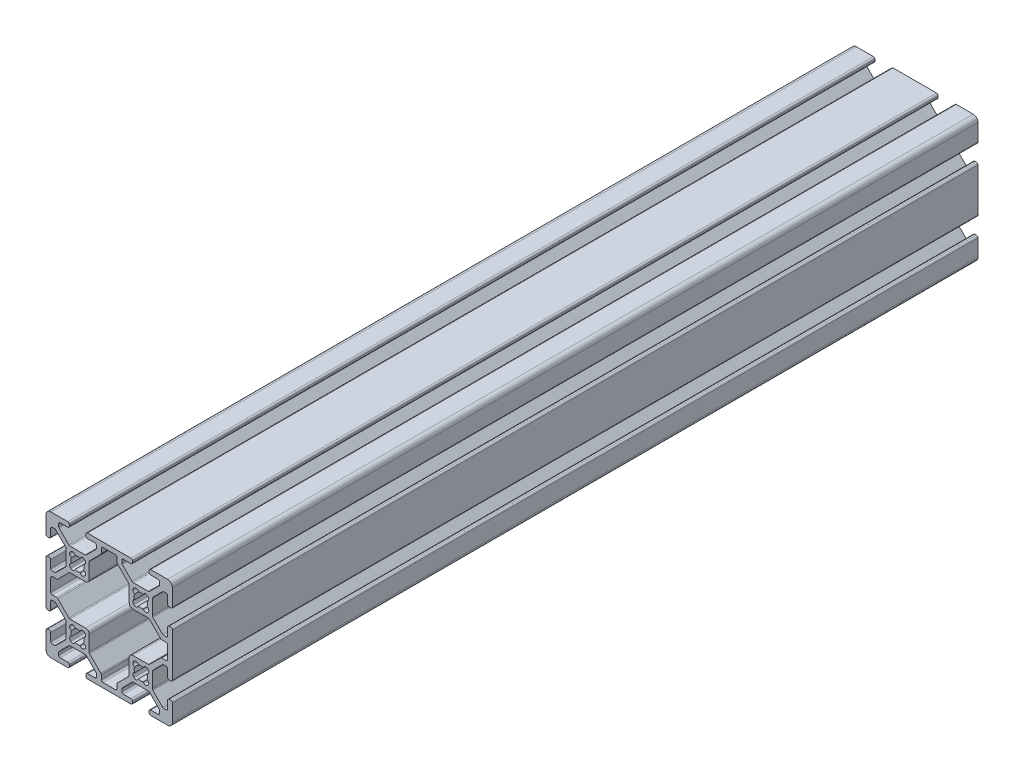
SolidWorks part; units mm, degrees
material "6105-T5 Aluminum"
ref_plane "Front Plane" through (0, 0, 0) normal (0, 0, 1) x (1, 0, 0)
ref_plane "Top Plane" through (0, 0, 0) normal (0, 1, 0) x (1, 0, 0)
ref_plane "Right Plane" through (0, 0, 0) normal (1, 0, 0) x (0, 0, -1)
sketch "Sketch1" plane through (0, 0, 0) normal (0, 0, 1) x (1, 0, 0)
  line L0 (-2.1249, 17.6955) -> (-2.3045, 17.8751)
  line L1 (-2.3045, 22.1249) -> (-2.1249, 22.3045)
  line L2 (2.1249, 22.3045) -> (2.3045, 22.1249)
  line L3 (2.3045, 17.8751) -> (2.1249, 17.6955)
  line L4 (-22.1249, 17.6955) -> (-22.3045, 17.8751)
  line L5 (-22.3045, 22.1249) -> (-22.1249, 22.3045)
  line L6 (-17.8751, 22.3045) -> (-17.6955, 22.1249)
  line L7 (-17.6955, 17.8751) -> (-17.8751, 17.6955)
  line L8 (-2.1249, -2.3045) -> (-2.3045, -2.1249)
  line L9 (-2.3045, 2.1249) -> (-2.1249, 2.3045)
  line L10 (2.1249, 2.3045) -> (2.3045, 2.1249)
  line L11 (2.3045, -2.1249) -> (2.1249, -2.3045)
  line L12 (-12.505, -7.992) -> (-12.505, -6.6448)
  line L13 (-12.6538, -6.2856) -> (-16.1962, -2.7431)
  line L14 (-16.345, -2.3839) -> (-16.345, 2.512)
  line L15 (-17.488, 3.655) -> (-22.3839, 3.655)
  line L16 (-22.7431, 3.8038) -> (-26.2856, 7.3462)
  line L17 (-26.6448, 7.495) -> (-27.992, 7.495)
  line L18 (-28.5, 8.003) -> (-28.5, 11.997)
  line L19 (-27.992, 12.505) -> (-26.6448, 12.505)
  line L20 (-26.2856, 12.6538) -> (-22.7431, 16.1962)
  line L21 (-22.3839, 16.345) -> (-17.488, 16.345)
  line L22 (-16.345, 17.488) -> (-16.345, 22.3839)
  line L23 (-16.1962, 22.7431) -> (-12.6538, 26.2856)
  line L24 (-12.505, 26.6448) -> (-12.505, 27.992)
  line L25 (-11.997, 28.5) -> (-8.003, 28.5)
  line L26 (-7.495, 27.992) -> (-7.495, 26.6448)
  line L27 (-7.3462, 26.2856) -> (-3.8038, 22.7431)
  line L28 (-3.655, 22.3839) -> (-3.655, 17.488)
  line L29 (-2.512, 16.345) -> (2.3839, 16.345)
  line L30 (2.7431, 16.1962) -> (6.2856, 12.6538)
  line L31 (6.6448, 12.505) -> (7.992, 12.505)
  line L32 (8.5, 11.997) -> (8.5, 8.003)
  line L33 (7.992, 7.495) -> (6.6448, 7.495)
  line L34 (6.2856, 7.3462) -> (2.7431, 3.8038)
  line L35 (2.3839, 3.655) -> (-2.512, 3.655)
  line L36 (-3.655, 2.512) -> (-3.655, -2.3839)
  line L37 (-3.8038, -2.7431) -> (-7.3462, -6.2856)
  line L38 (-7.495, -6.6448) -> (-7.495, -7.992)
  line L39 (-8.003, -8.5) -> (-11.997, -8.5)
  line L40 (-22.1249, -2.3045) -> (-22.3045, -2.1249)
  line L41 (-22.3045, 2.1249) -> (-22.1249, 2.3045)
  line L42 (-17.8751, 2.3045) -> (-17.6955, 2.1249)
  line L43 (-17.6955, -2.1249) -> (-17.8751, -2.3045)
  line L44 (-22.3839, -3.655) -> (-17.6161, -3.655)
  line L45 (-17.2569, -3.8038) -> (-14.1538, -6.9069)
  line L46 (-14.005, -7.2661) -> (-14.005, -7.992)
  line L47 (-14.513, -8.5) -> (-16.862, -8.5)
  line L48 (-17.37, -9.008) -> (-17.37, -9.492)
  line L49 (-16.862, -10) -> (-3.138, -10)
  line L50 (-2.63, -9.492) -> (-2.63, -9.008)
  line L51 (-3.138, -8.5) -> (-5.487, -8.5)
  line L52 (-5.995, -7.992) -> (-5.995, -7.2661)
  line L53 (-5.8462, -6.9069) -> (-2.7431, -3.8038)
  line L54 (-2.3839, -3.655) -> (2.3839, -3.655)
  line L55 (2.7431, -3.8038) -> (5.8462, -6.9069)
  line L56 (5.995, -7.2661) -> (5.995, -7.992)
  line L57 (5.487, -8.5) -> (3.138, -8.5)
  line L58 (2.63, -9.008) -> (2.63, -9.492)
  line L59 (3.138, -10) -> (8.5, -10)
  line L60 (10, -8.5) -> (10, -3.138)
  line L61 (9.492, -2.63) -> (9.008, -2.63)
  line L62 (8.5, -3.138) -> (8.5, -5.487)
  line L63 (7.992, -5.995) -> (7.2661, -5.995)
  line L64 (6.9069, -5.8462) -> (3.8038, -2.7431)
  line L65 (3.655, -2.3839) -> (3.655, 2.3839)
  line L66 (3.8038, 2.7431) -> (6.9069, 5.8462)
  line L67 (7.2661, 5.995) -> (7.992, 5.995)
  line L68 (8.5, 5.487) -> (8.5, 3.138)
  line L69 (9.008, 2.63) -> (9.492, 2.63)
  line L70 (10, 3.138) -> (10, 16.862)
  line L71 (9.492, 17.37) -> (9.008, 17.37)
  line L72 (8.5, 16.862) -> (8.5, 14.513)
  line L73 (7.992, 14.005) -> (7.2661, 14.005)
  line L74 (6.9069, 14.1538) -> (3.8038, 17.2569)
  line L75 (3.655, 17.6161) -> (3.655, 22.3839)
  line L76 (3.8038, 22.7431) -> (6.9069, 25.8462)
  line L77 (7.2661, 25.995) -> (7.992, 25.995)
  line L78 (8.5, 25.487) -> (8.5, 23.138)
  line L79 (9.008, 22.63) -> (9.492, 22.63)
  line L80 (10, 23.138) -> (10, 28.5)
  line L81 (8.5, 30) -> (3.138, 30)
  line L82 (2.63, 29.492) -> (2.63, 29.008)
  line L83 (3.138, 28.5) -> (5.487, 28.5)
  line L84 (5.995, 27.992) -> (5.995, 27.2661)
  line L85 (5.8462, 26.9069) -> (2.7431, 23.8038)
  line L86 (2.3839, 23.655) -> (-2.3839, 23.655)
  line L87 (-2.7431, 23.8038) -> (-5.8462, 26.9069)
  line L88 (-5.995, 27.2661) -> (-5.995, 27.992)
  line L89 (-5.487, 28.5) -> (-3.138, 28.5)
  line L90 (-2.63, 29.008) -> (-2.63, 29.492)
  line L91 (-3.138, 30) -> (-16.862, 30)
  line L92 (-17.37, 29.492) -> (-17.37, 29.008)
  line L93 (-16.862, 28.5) -> (-14.513, 28.5)
  line L94 (-14.005, 27.992) -> (-14.005, 27.2661)
  line L95 (-14.1538, 26.9069) -> (-17.2569, 23.8038)
  line L96 (-17.6161, 23.655) -> (-22.3839, 23.655)
  line L97 (-22.7431, 23.8038) -> (-25.8462, 26.9069)
  line L98 (-25.995, 27.2661) -> (-25.995, 27.992)
  line L99 (-25.487, 28.5) -> (-23.138, 28.5)
  line L100 (-22.63, 29.008) -> (-22.63, 29.492)
  line L101 (-23.138, 30) -> (-28.5, 30)
  line L102 (-30, 28.5) -> (-30, 23.138)
  line L103 (-29.492, 22.63) -> (-29.008, 22.63)
  line L104 (-28.5, 23.138) -> (-28.5, 25.487)
  line L105 (-27.992, 25.995) -> (-27.2661, 25.995)
  line L106 (-26.9069, 25.8462) -> (-23.8038, 22.7431)
  line L107 (-23.655, 22.3839) -> (-23.655, 17.6161)
  line L108 (-23.8038, 17.2569) -> (-26.9069, 14.1538)
  line L109 (-27.2661, 14.005) -> (-27.992, 14.005)
  line L110 (-28.5, 14.513) -> (-28.5, 16.862)
  line L111 (-29.008, 17.37) -> (-29.492, 17.37)
  line L112 (-30, 16.862) -> (-30, 3.138)
  line L113 (-29.492, 2.63) -> (-29.008, 2.63)
  line L114 (-28.5, 3.138) -> (-28.5, 5.487)
  line L115 (-27.992, 5.995) -> (-27.2661, 5.995)
  line L116 (-26.9069, 5.8462) -> (-23.8038, 2.7431)
  line L117 (-23.655, 2.3839) -> (-23.655, -2.3839)
  line L118 (-23.8038, -2.7431) -> (-26.9069, -5.8462)
  line L119 (-27.2661, -5.995) -> (-27.992, -5.995)
  line L120 (-28.5, -5.487) -> (-28.5, -3.138)
  line L121 (-29.008, -2.63) -> (-29.492, -2.63)
  line L122 (-30, -3.138) -> (-30, -8.5)
  line L123 (-28.5, -10) -> (-23.138, -10)
  line L124 (-22.63, -9.492) -> (-22.63, -9.008)
  line L125 (-23.138, -8.5) -> (-25.487, -8.5)
  line L126 (-25.995, -7.992) -> (-25.995, -7.2661)
  line L127 (-25.8462, -6.9069) -> (-22.7431, -3.8038)
  arc A0 (-1.9351, 19.196) -> (-2.3045, 17.8751) centre (-1.748, 18.4316) ccw
  arc A1 (-1.9351, 20.804) -> (-1.9351, 19.196) centre (0, 20) ccw
  arc A2 (-2.3045, 22.1249) -> (-1.9351, 20.804) centre (-1.748, 21.5684) ccw
  arc A3 (-0.804, 21.9351) -> (-2.1249, 22.3045) centre (-1.5684, 21.748) ccw
  arc A4 (0.804, 21.9351) -> (-0.804, 21.9351) centre (0, 20) ccw
  arc A5 (2.1249, 22.3045) -> (0.804, 21.9351) centre (1.5684, 21.748) ccw
  arc A6 (1.9351, 20.804) -> (2.3045, 22.1249) centre (1.748, 21.5684) ccw
  arc A7 (1.9351, 19.196) -> (1.9351, 20.804) centre (0, 20) ccw
  arc A8 (2.3045, 17.8751) -> (1.9351, 19.196) centre (1.748, 18.4316) ccw
  arc A9 (0.804, 18.0649) -> (2.1249, 17.6955) centre (1.5684, 18.252) ccw
  arc A10 (-0.804, 18.0649) -> (0.804, 18.0649) centre (0, 20) ccw
  arc A11 (-2.1249, 17.6955) -> (-0.804, 18.0649) centre (-1.5684, 18.252) ccw
  arc A12 (-21.9351, 19.196) -> (-22.3045, 17.8751) centre (-21.748, 18.4316) ccw
  arc A13 (-21.9351, 20.804) -> (-21.9351, 19.196) centre (-20, 20) ccw
  arc A14 (-22.3045, 22.1249) -> (-21.9351, 20.804) centre (-21.748, 21.5684) ccw
  arc A15 (-20.804, 21.9351) -> (-22.1249, 22.3045) centre (-21.5684, 21.748) ccw
  arc A16 (-19.196, 21.9351) -> (-20.804, 21.9351) centre (-20, 20) ccw
  arc A17 (-17.8751, 22.3045) -> (-19.196, 21.9351) centre (-18.4316, 21.748) ccw
  arc A18 (-18.0649, 20.804) -> (-17.6955, 22.1249) centre (-18.252, 21.5684) ccw
  arc A19 (-18.0649, 19.196) -> (-18.0649, 20.804) centre (-20, 20) ccw
  arc A20 (-17.6955, 17.8751) -> (-18.0649, 19.196) centre (-18.252, 18.4316) ccw
  arc A21 (-19.196, 18.0649) -> (-17.8751, 17.6955) centre (-18.4316, 18.252) ccw
  arc A22 (-20.804, 18.0649) -> (-19.196, 18.0649) centre (-20, 20) ccw
  arc A23 (-22.1249, 17.6955) -> (-20.804, 18.0649) centre (-21.5684, 18.252) ccw
  arc A24 (-1.9351, -0.804) -> (-2.3045, -2.1249) centre (-1.748, -1.5684) ccw
  arc A25 (-1.9351, 0.804) -> (-1.9351, -0.804) centre (0, 0) ccw
  arc A26 (-2.3045, 2.1249) -> (-1.9351, 0.804) centre (-1.748, 1.5684) ccw
  arc A27 (-0.804, 1.9351) -> (-2.1249, 2.3045) centre (-1.5684, 1.748) ccw
  arc A28 (0.804, 1.9351) -> (-0.804, 1.9351) centre (0, 0) ccw
  arc A29 (2.1249, 2.3045) -> (0.804, 1.9351) centre (1.5684, 1.748) ccw
  arc A30 (1.9351, 0.804) -> (2.3045, 2.1249) centre (1.748, 1.5684) ccw
  arc A31 (1.9351, -0.804) -> (1.9351, 0.804) centre (0, 0) ccw
  arc A32 (2.3045, -2.1249) -> (1.9351, -0.804) centre (1.748, -1.5684) ccw
  arc A33 (0.804, -1.9351) -> (2.1249, -2.3045) centre (1.5684, -1.748) ccw
  arc A34 (-0.804, -1.9351) -> (0.804, -1.9351) centre (0, 0) ccw
  arc A35 (-2.1249, -2.3045) -> (-0.804, -1.9351) centre (-1.5684, -1.748) ccw
  arc A36 (-12.505, -7.992) -> (-11.997, -8.5) centre (-11.997, -7.992) ccw
  arc A37 (-12.505, -6.6448) -> (-12.6538, -6.2856) centre (-13.013, -6.6448) ccw
  arc A38 (-16.345, -2.3839) -> (-16.1962, -2.7431) centre (-15.837, -2.3839) ccw
  arc A39 (-16.345, 2.512) -> (-17.488, 3.655) centre (-17.488, 2.512) ccw
  arc A40 (-22.7431, 3.8038) -> (-22.3839, 3.655) centre (-22.3839, 4.163) ccw
  arc A41 (-26.2856, 7.3462) -> (-26.6448, 7.495) centre (-26.6448, 6.987) ccw
  arc A42 (-28.5, 8.003) -> (-27.992, 7.495) centre (-27.992, 8.003) ccw
  arc A43 (-27.992, 12.505) -> (-28.5, 11.997) centre (-27.992, 11.997) ccw
  arc A44 (-26.6448, 12.505) -> (-26.2856, 12.6538) centre (-26.6448, 13.013) ccw
  arc A45 (-22.3839, 16.345) -> (-22.7431, 16.1962) centre (-22.3839, 15.837) ccw
  arc A46 (-17.488, 16.345) -> (-16.345, 17.488) centre (-17.488, 17.488) ccw
  arc A47 (-16.1962, 22.7431) -> (-16.345, 22.3839) centre (-15.837, 22.3839) ccw
  arc A48 (-12.6538, 26.2856) -> (-12.505, 26.6448) centre (-13.013, 26.6448) ccw
  arc A49 (-11.997, 28.5) -> (-12.505, 27.992) centre (-11.997, 27.992) ccw
  arc A50 (-7.495, 27.992) -> (-8.003, 28.5) centre (-8.003, 27.992) ccw
  arc A51 (-7.495, 26.6448) -> (-7.3462, 26.2856) centre (-6.987, 26.6448) ccw
  arc A52 (-3.655, 22.3839) -> (-3.8038, 22.7431) centre (-4.163, 22.3839) ccw
  arc A53 (-3.655, 17.488) -> (-2.512, 16.345) centre (-2.512, 17.488) ccw
  arc A54 (2.7431, 16.1962) -> (2.3839, 16.345) centre (2.3839, 15.837) ccw
  arc A55 (6.2856, 12.6538) -> (6.6448, 12.505) centre (6.6448, 13.013) ccw
  arc A56 (8.5, 11.997) -> (7.992, 12.505) centre (7.992, 11.997) ccw
  arc A57 (7.992, 7.495) -> (8.5, 8.003) centre (7.992, 8.003) ccw
  arc A58 (6.6448, 7.495) -> (6.2856, 7.3462) centre (6.6448, 6.987) ccw
  arc A59 (2.3839, 3.655) -> (2.7431, 3.8038) centre (2.3839, 4.163) ccw
  arc A60 (-2.512, 3.655) -> (-3.655, 2.512) centre (-2.512, 2.512) ccw
  arc A61 (-3.8038, -2.7431) -> (-3.655, -2.3839) centre (-4.163, -2.3839) ccw
  arc A62 (-7.3462, -6.2856) -> (-7.495, -6.6448) centre (-6.987, -6.6448) ccw
  arc A63 (-8.003, -8.5) -> (-7.495, -7.992) centre (-8.003, -7.992) ccw
  arc A64 (-21.9351, -0.804) -> (-22.3045, -2.1249) centre (-21.748, -1.5684) ccw
  arc A65 (-21.9351, 0.804) -> (-21.9351, -0.804) centre (-20, 0) ccw
  arc A66 (-22.3045, 2.1249) -> (-21.9351, 0.804) centre (-21.748, 1.5684) ccw
  arc A67 (-20.804, 1.9351) -> (-22.1249, 2.3045) centre (-21.5684, 1.748) ccw
  arc A68 (-19.196, 1.9351) -> (-20.804, 1.9351) centre (-20, 0) ccw
  arc A69 (-17.8751, 2.3045) -> (-19.196, 1.9351) centre (-18.4316, 1.748) ccw
  arc A70 (-18.0649, 0.804) -> (-17.6955, 2.1249) centre (-18.252, 1.5684) ccw
  arc A71 (-18.0649, -0.804) -> (-18.0649, 0.804) centre (-20, 0) ccw
  arc A72 (-17.6955, -2.1249) -> (-18.0649, -0.804) centre (-18.252, -1.5684) ccw
  arc A73 (-19.196, -1.9351) -> (-17.8751, -2.3045) centre (-18.4316, -1.748) ccw
  arc A74 (-20.804, -1.9351) -> (-19.196, -1.9351) centre (-20, 0) ccw
  arc A75 (-22.1249, -2.3045) -> (-20.804, -1.9351) centre (-21.5684, -1.748) ccw
  arc A76 (-22.3839, -3.655) -> (-22.7431, -3.8038) centre (-22.3839, -4.163) ccw
  arc A77 (-17.2569, -3.8038) -> (-17.6161, -3.655) centre (-17.6161, -4.163) ccw
  arc A78 (-14.005, -7.2661) -> (-14.1538, -6.9069) centre (-14.513, -7.2661) ccw
  arc A79 (-14.513, -8.5) -> (-14.005, -7.992) centre (-14.513, -7.992) ccw
  arc A80 (-16.862, -8.5) -> (-17.37, -9.008) centre (-16.862, -9.008) ccw
  arc A81 (-17.37, -9.492) -> (-16.862, -10) centre (-16.862, -9.492) ccw
  arc A82 (-3.138, -10) -> (-2.63, -9.492) centre (-3.138, -9.492) ccw
  arc A83 (-2.63, -9.008) -> (-3.138, -8.5) centre (-3.138, -9.008) ccw
  arc A84 (-5.995, -7.992) -> (-5.487, -8.5) centre (-5.487, -7.992) ccw
  arc A85 (-5.8462, -6.9069) -> (-5.995, -7.2661) centre (-5.487, -7.2661) ccw
  arc A86 (-2.3839, -3.655) -> (-2.7431, -3.8038) centre (-2.3839, -4.163) ccw
  arc A87 (2.7431, -3.8038) -> (2.3839, -3.655) centre (2.3839, -4.163) ccw
  arc A88 (5.995, -7.2661) -> (5.8462, -6.9069) centre (5.487, -7.2661) ccw
  arc A89 (5.487, -8.5) -> (5.995, -7.992) centre (5.487, -7.992) ccw
  arc A90 (3.138, -8.5) -> (2.63, -9.008) centre (3.138, -9.008) ccw
  arc A91 (2.63, -9.492) -> (3.138, -10) centre (3.138, -9.492) ccw
  arc A92 (8.5, -10) -> (10, -8.5) centre (8.5, -8.5) ccw
  arc A93 (10, -3.138) -> (9.492, -2.63) centre (9.492, -3.138) ccw
  arc A94 (9.008, -2.63) -> (8.5, -3.138) centre (9.008, -3.138) ccw
  arc A95 (7.992, -5.995) -> (8.5, -5.487) centre (7.992, -5.487) ccw
  arc A96 (6.9069, -5.8462) -> (7.2661, -5.995) centre (7.2661, -5.487) ccw
  arc A97 (3.655, -2.3839) -> (3.8038, -2.7431) centre (4.163, -2.3839) ccw
  arc A98 (3.8038, 2.7431) -> (3.655, 2.3839) centre (4.163, 2.3839) ccw
  arc A99 (7.2661, 5.995) -> (6.9069, 5.8462) centre (7.2661, 5.487) ccw
  arc A100 (8.5, 5.487) -> (7.992, 5.995) centre (7.992, 5.487) ccw
  arc A101 (8.5, 3.138) -> (9.008, 2.63) centre (9.008, 3.138) ccw
  arc A102 (9.492, 2.63) -> (10, 3.138) centre (9.492, 3.138) ccw
  arc A103 (10, 16.862) -> (9.492, 17.37) centre (9.492, 16.862) ccw
  arc A104 (9.008, 17.37) -> (8.5, 16.862) centre (9.008, 16.862) ccw
  arc A105 (7.992, 14.005) -> (8.5, 14.513) centre (7.992, 14.513) ccw
  arc A106 (6.9069, 14.1538) -> (7.2661, 14.005) centre (7.2661, 14.513) ccw
  arc A107 (3.655, 17.6161) -> (3.8038, 17.2569) centre (4.163, 17.6161) ccw
  arc A108 (3.8038, 22.7431) -> (3.655, 22.3839) centre (4.163, 22.3839) ccw
  arc A109 (7.2661, 25.995) -> (6.9069, 25.8462) centre (7.2661, 25.487) ccw
  arc A110 (8.5, 25.487) -> (7.992, 25.995) centre (7.992, 25.487) ccw
  arc A111 (8.5, 23.138) -> (9.008, 22.63) centre (9.008, 23.138) ccw
  arc A112 (9.492, 22.63) -> (10, 23.138) centre (9.492, 23.138) ccw
  arc A113 (10, 28.5) -> (8.5, 30) centre (8.5, 28.5) ccw
  arc A114 (3.138, 30) -> (2.63, 29.492) centre (3.138, 29.492) ccw
  arc A115 (2.63, 29.008) -> (3.138, 28.5) centre (3.138, 29.008) ccw
  arc A116 (5.995, 27.992) -> (5.487, 28.5) centre (5.487, 27.992) ccw
  arc A117 (5.8462, 26.9069) -> (5.995, 27.2661) centre (5.487, 27.2661) ccw
  arc A118 (2.3839, 23.655) -> (2.7431, 23.8038) centre (2.3839, 24.163) ccw
  arc A119 (-2.7431, 23.8038) -> (-2.3839, 23.655) centre (-2.3839, 24.163) ccw
  arc A120 (-5.995, 27.2661) -> (-5.8462, 26.9069) centre (-5.487, 27.2661) ccw
  arc A121 (-5.487, 28.5) -> (-5.995, 27.992) centre (-5.487, 27.992) ccw
  arc A122 (-3.138, 28.5) -> (-2.63, 29.008) centre (-3.138, 29.008) ccw
  arc A123 (-2.63, 29.492) -> (-3.138, 30) centre (-3.138, 29.492) ccw
  arc A124 (-16.862, 30) -> (-17.37, 29.492) centre (-16.862, 29.492) ccw
  arc A125 (-17.37, 29.008) -> (-16.862, 28.5) centre (-16.862, 29.008) ccw
  arc A126 (-14.005, 27.992) -> (-14.513, 28.5) centre (-14.513, 27.992) ccw
  arc A127 (-14.1538, 26.9069) -> (-14.005, 27.2661) centre (-14.513, 27.2661) ccw
  arc A128 (-17.6161, 23.655) -> (-17.2569, 23.8038) centre (-17.6161, 24.163) ccw
  arc A129 (-22.7431, 23.8038) -> (-22.3839, 23.655) centre (-22.3839, 24.163) ccw
  arc A130 (-25.995, 27.2661) -> (-25.8462, 26.9069) centre (-25.487, 27.2661) ccw
  arc A131 (-25.487, 28.5) -> (-25.995, 27.992) centre (-25.487, 27.992) ccw
  arc A132 (-23.138, 28.5) -> (-22.63, 29.008) centre (-23.138, 29.008) ccw
  arc A133 (-22.63, 29.492) -> (-23.138, 30) centre (-23.138, 29.492) ccw
  arc A134 (-28.5, 30) -> (-30, 28.5) centre (-28.5, 28.5) ccw
  arc A135 (-30, 23.138) -> (-29.492, 22.63) centre (-29.492, 23.138) ccw
  arc A136 (-29.008, 22.63) -> (-28.5, 23.138) centre (-29.008, 23.138) ccw
  arc A137 (-27.992, 25.995) -> (-28.5, 25.487) centre (-27.992, 25.487) ccw
  arc A138 (-26.9069, 25.8462) -> (-27.2661, 25.995) centre (-27.2661, 25.487) ccw
  arc A139 (-23.655, 22.3839) -> (-23.8038, 22.7431) centre (-24.163, 22.3839) ccw
  arc A140 (-23.8038, 17.2569) -> (-23.655, 17.6161) centre (-24.163, 17.6161) ccw
  arc A141 (-27.2661, 14.005) -> (-26.9069, 14.1538) centre (-27.2661, 14.513) ccw
  arc A142 (-28.5, 14.513) -> (-27.992, 14.005) centre (-27.992, 14.513) ccw
  arc A143 (-28.5, 16.862) -> (-29.008, 17.37) centre (-29.008, 16.862) ccw
  arc A144 (-29.492, 17.37) -> (-30, 16.862) centre (-29.492, 16.862) ccw
  arc A145 (-30, 3.138) -> (-29.492, 2.63) centre (-29.492, 3.138) ccw
  arc A146 (-29.008, 2.63) -> (-28.5, 3.138) centre (-29.008, 3.138) ccw
  arc A147 (-27.992, 5.995) -> (-28.5, 5.487) centre (-27.992, 5.487) ccw
  arc A148 (-26.9069, 5.8462) -> (-27.2661, 5.995) centre (-27.2661, 5.487) ccw
  arc A149 (-23.655, 2.3839) -> (-23.8038, 2.7431) centre (-24.163, 2.3839) ccw
  arc A150 (-23.8038, -2.7431) -> (-23.655, -2.3839) centre (-24.163, -2.3839) ccw
  arc A151 (-27.2661, -5.995) -> (-26.9069, -5.8462) centre (-27.2661, -5.487) ccw
  arc A152 (-28.5, -5.487) -> (-27.992, -5.995) centre (-27.992, -5.487) ccw
  arc A153 (-28.5, -3.138) -> (-29.008, -2.63) centre (-29.008, -3.138) ccw
  arc A154 (-29.492, -2.63) -> (-30, -3.138) centre (-29.492, -3.138) ccw
  arc A155 (-30, -8.5) -> (-28.5, -10) centre (-28.5, -8.5) ccw
  arc A156 (-23.138, -10) -> (-22.63, -9.492) centre (-23.138, -9.492) ccw
  arc A157 (-22.63, -9.008) -> (-23.138, -8.5) centre (-23.138, -9.008) ccw
  arc A158 (-25.995, -7.992) -> (-25.487, -8.5) centre (-25.487, -7.992) ccw
  arc A159 (-25.8462, -6.9069) -> (-25.995, -7.2661) centre (-25.487, -7.2661) ccw
extrude "Extrude1" add sketch "Sketch1" against normal blind 255
